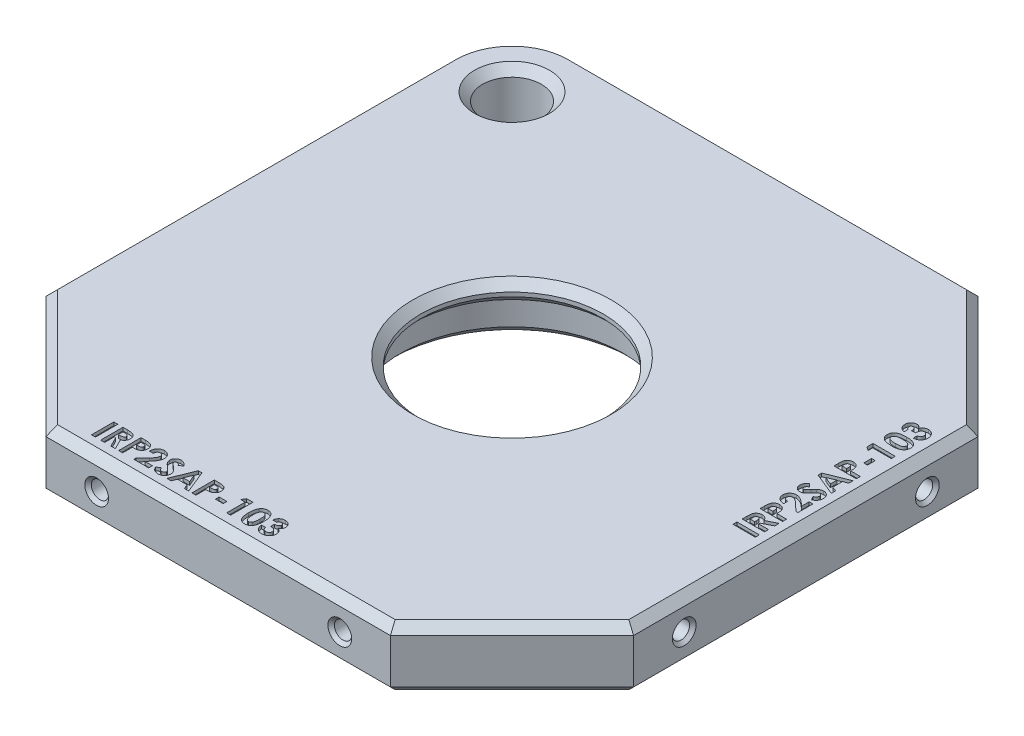
SolidWorks part; units mm, degrees
material "6061-T6 (SS)"
ref_plane "Front" through (0, 0, 0) normal (0, 0, 1) x (1, 0, 0)
ref_plane "Top" through (0, 0, 0) normal (0, 1, 0) x (1, 0, 0)
ref_plane "Right" through (0, 0, 0) normal (1, 0, 0) x (0, 0, -1)
sketch "Sketch1" plane through (0, 0, 0) normal (0, 1, 0) x (1, 0, 0)
  line L0 (0, 46.0375) -> (46.0375, 46.0375) construction
  line L1 (0, 0) -> (92.075, 0)
  line L2 (0, 0) -> (0, 92.075)
  line L3 (0, 92.075) -> (92.075, 92.075)
  line L4 (92.075, 0) -> (92.075, 92.075)
  line L5 (46.0375, 46.0375) -> (46.0375, 92.075) construction
  line L6 (10.033, 82.042) -> (0, 82.042) construction
  line L7 (10.033, 82.042) -> (10.033, 92.075) construction
  line L9 (17.3653, 82.042) -> (13.6992, 88.392) construction
  line L10 (13.6992, 88.392) -> (6.3668, 88.392) construction
  line L11 (6.3668, 88.392) -> (2.7007, 82.042) construction
  line L12 (2.7007, 82.042) -> (6.3668, 75.692) construction
  line L13 (6.3668, 75.692) -> (13.6992, 75.692) construction
  line L14 (13.6992, 75.692) -> (17.3653, 82.042) construction
  circle A0 centre (46.0375, 46.0375) radius 14.2875
  circle A1 centre (10.033, 82.042) radius 4.6037
  circle A2 centre (10.033, 82.042) radius 6.35 construction
  dimension "D2" = 28.575
  dimension "D3" = 9.2075
  dimension "D1" = 92.075
  dimension "D4" = 10.033
  dimension "D5" = 12.7
extrude "Boss-Extrude1" add sketch "Sketch1" along normal blind 9.525
chamfer "Chamfer1" distance 19.05 angle 45 3 edges at (92.075, 4.7625, 0) (0, 4.7625, 0) (92.075, 4.7625, -92.075)
hole_wizard "#6-32 Tapped Hole1" positions "Sketch2" profile "Sketch3" tap size "#6-32" standard "ANSI Inch"
sketch "Sketch2" plane through (0, 0, 0) normal (0, 0, 1) x (1, 0, 0)
  line L6 (0, 4.7625) -> (26.9875, 4.7625) construction
  line L7 (0, 9.525) -> (0, 0) construction
  line L8 (26.9875, 4.7625) -> (65.0875, 4.7625) construction
  line L9 (65.0875, 4.7625) -> (92.075, 4.7625) construction
  line L10 (92.075, 9.525) -> (92.075, 0) construction
  point P26 (26.9875, 4.7625)
  point P30 (65.0875, 4.7625)
  dimension "D1" = 38.1
sketch "Sketch3" plane through (65.0875, 4.7625, 0) normal (1, 0, 0) x (0, -1, 0)
  line L0 (0, 0) -> (0, 13.5127)
  line L1 (0, 13.5127) -> (1.3525, 12.7)
  line L2 (1.3525, 12.7) -> (1.3525, 0)
  line L5 (1.3525, 0) -> (0, 0)
  line L10 (0, 13.5127) -> (-1.3526, 12.7) construction
  line L11 (0, -6.35) -> (0, 107.95) construction
  dimension "Tap Drill Dia." = 2.7051
  dimension "Tap Drill Depth" = 12.7
  dimension "Drill Angle" = 118
cosmetic thread "Hole Thread1" parameters "D1"=11.43, "D2"=3.5052
cosmetic thread "Hole Thread2" parameters "D1"=11.43, "D2"=3.5052
ref_plane "Plane1" through (46.0375, 0, -46.0375) normal (-0.7071, 0, 0.7071) x (0.7071, 0, 0.7071)
mirror "Mirror1" about plane through (46.0375, 0, -46.0375) normal (-0.7071, 0, 0.7071) of "#6-32 Tapped Hole1"
cosmetic thread "Hole Thread3" parameters "D1"=11.43, "D2"=3.5052
cosmetic thread "Hole Thread4" parameters "D1"=11.43, "D2"=3.5052
sketch "Sketch7" plane through (0, 0, 0) normal (0, -1, 0) x (1, 0, 0)
  circle A0 centre (46.0375, -46.0375) radius 17.5
  dimension "D1" = 34.9999
extrude "Cut-Extrude2" cut sketch "Sketch7" against normal blind 6.35
fillet "Fillet1" radius 10.033 1 edges at (0, 4.7625, -92.075)
chamfer "Chamfer2" distance 1.27 angle 45 19 edges at (46.0375, 9.525, -31.75) (0, 0, -50.546) (41.529, 0, -92.075) (92.075, 0, -46.0375) (82.55, 0, -9.525) (46.0375, 0, 0) (0, 9.525, -50.546) (41.529, 9.525, -92.075) (92.075, 9.525, -46.0375) (82.55, 9.525, -9.525) (46.0375, 9.525, 0) (10.033, 0, -77.4383) (10.033, 9.525, -77.4383) (82.55, 9.525, -82.55) (9.525, 9.525, -9.525) (2.9386, 9.525, -89.1364) (2.9386, 0, -89.1364) (46.0375, 6.35, -60.325) (46.0375, 0, -63.5375)
chamfer "Chamfer3" distance 0.508 angle 45 4 edges at (92.075, 4.7625, -66.4401) (92.075, 4.7625, -28.34) (66.44, 4.7625, 0) (28.34, 4.7625, 0)
sketch "Sketch4" plane through (0, 9.525, 0) normal (0, 1, 0) x (1, 0, 0)
  line L0 (1.27, 2.54) -> (73.7689, 2.54) construction
  line L1 (1.27, 82.042) -> (1.27, 19.5761) construction
  line L2 (72.4989, 1.27) -> (90.805, 19.5761) construction
  line L3 (89.535, 18.3061) -> (89.535, 90.805) construction
  line L4 (72.4989, 90.805) -> (10.033, 90.805) construction
  line L5 (90.805, 19.5761) -> (90.805, 72.4989) construction
  text T0 "<b>IRP2SAP-103</b>"
  text T1 "<b>IRP2SAP-103</b>"
  dimension "D1" = 1.27
extrude "Cut-Extrude1" cut sketch "Sketch4" against normal blind 0.508
